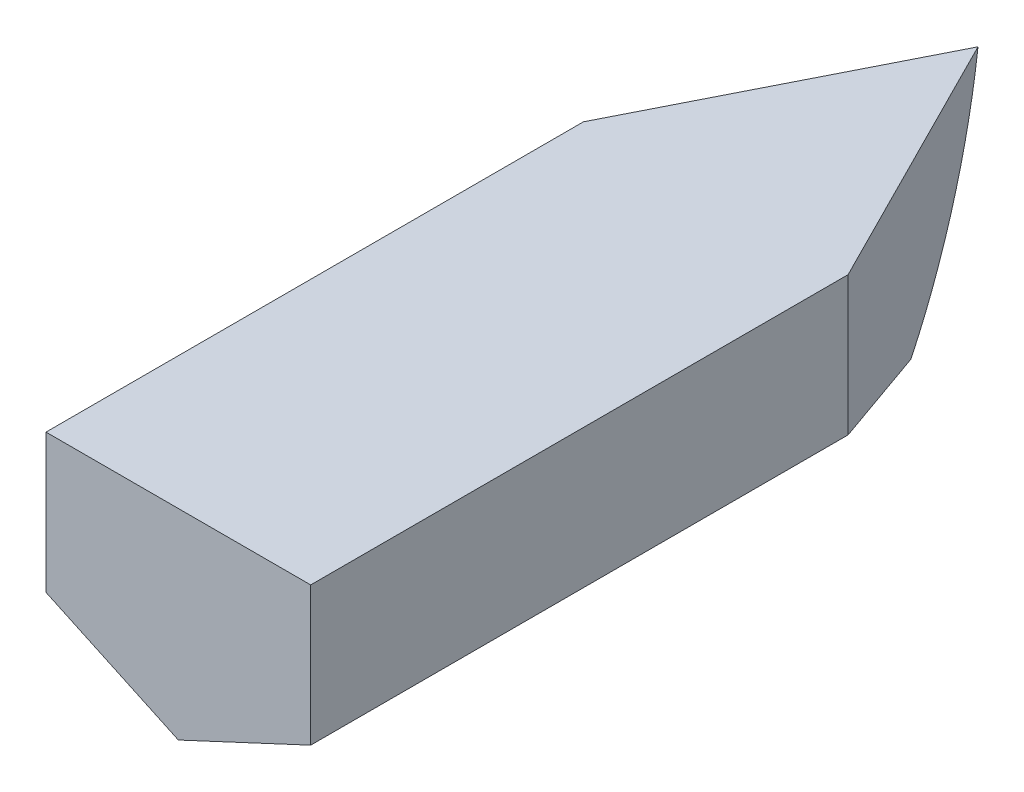
SolidWorks part; units mm, degrees
material "Rubber"
ref_plane "Front Plane" through (0, 0, 0) normal (0, 0, 1) x (1, 0, 0)
ref_plane "Top Plane" through (0, 0, 0) normal (0, 1, 0) x (1, 0, 0)
ref_plane "Right Plane" through (0, 0, 0) normal (1, 0, 0) x (0, 0, -1)
sketch "Cross-Section B Sketch" plane through (0, 0, 0) normal (0, 0, 1) x (1, 0, 0)
  line L5 (-0.0006, -30.4064) -> (37.5282, -12.9064)
  line L6 (37.5282, -12.9064) -> (37.5282, 26.4536)
  line L7 (37.5282, 26.4536) -> (-37.5294, 26.4536)
  line L8 (-37.5294, -12.9064) -> (-37.5294, 26.4536)
  line L9 (-0.0006, -30.4064) -> (-37.5294, -12.9064)
  line L10 (-76.707, -30.4064) -> (84.3947, -30.4064) construction
  dimension "Deadrise Angle" = 25
  dimension "Width" = 75.0576
  dimension "Height" = 56.86
sketch "Fore-Aft" plane through (0, 0, 0) normal (1, 0, 0) x (0, 0, -1)
  line L0 (0, 0) -> (62.0342, 0) construction
  line L1 (76.2, 28.4649) -> (-76.2, 28.4649)
  line L2 (151.4715, 28.4649) -> (76.2, 28.4649)
  line L4 (76.2, -30.4064) -> (-76.2, -30.4064)
  line L6 (-76.2, 28.4649) -> (-76.2, -30.4064)
  line L7 (76.2, -30.4064) -> (76.2, 28.4649)
  point P6 (0, 28.4649)
  point P9 (0, -30.4064)
  dimension "D1" = 152.4
  dimension "D2" = 58.8713
ref_plane "Cross-Section A Plane " through (0, 0, -76.2) normal (0, 0, -1) x (-1, 0, 0)
sketch "Cross-Section A Sketch" plane through (0, 0, -76.2) normal (0, 0, -1) x (-1, 0, 0)
  line L5 (-0.0006, -30.4064) -> (37.5282, -12.9064)
  line L6 (37.5282, -12.9064) -> (37.5282, 26.4536)
  line L7 (37.5282, 26.4536) -> (-37.5294, 26.4536)
  line L8 (-37.5294, -12.9064) -> (-37.5294, 26.4536)
  line L9 (-0.0006, -30.4064) -> (-37.5294, -12.9064)
  line L10 (-76.707, -30.4064) -> (84.3947, -30.4064) construction
  dimension "Deadrise Angle" = 25
  dimension "Width" = 75.0576
  dimension "Height" = 56.86
ref_plane "Cross-Section C Plane" through (0, 0, 76.2) normal (0, 0, -1) x (-1, 0, 0)
sketch "Cross-Section C Sketch" plane through (0, 0, 76.2) normal (0, 0, 1) x (1, 0, 0)
  line L5 (-0.0006, -30.4064) -> (37.5282, -12.9064)
  line L6 (37.5282, -12.9064) -> (37.5282, 26.4536)
  line L7 (37.5282, 26.4536) -> (-37.5294, 26.4536)
  line L8 (-37.5294, -12.9064) -> (-37.5294, 26.4536)
  line L9 (-0.0006, -30.4064) -> (-37.5294, -12.9064)
  line L10 (-76.707, -30.4064) -> (84.3947, -30.4064) construction
  dimension "Deadrise Angle" = 25
  dimension "Width" = 75.0576
  dimension "Height" = 56.86
loft "Fore-Aft Loft" add profiles "Cross-Section C Sketch", "Cross-Section B Sketch", "Cross-Section A Sketch"
sketch "Port-Starboard Profile" plane through (0, 0, 0) normal (1, 0, 0) x (0, 0, -1)
  line L4 (76.2, 26.4536) -> (-76.2, 26.4536) construction
  line L5 (76.2, 26.4536) -> (-76.2, 26.4536) construction
  line L7 (150.5603, 26.4536) -> (150.5603, -30.4064)
  line L8 (76.2, -30.4064) -> (150.5603, -30.4064)
  arc A1 (76.2, -30.4064) -> (150.5603, 26.4536) centre (75.8165, 47.1485) ccw
  dimension "Bow Curve Radius" = 77.5558
  dimension "Bow Length" = 74.3603
sketch "Top Bow Profile" plane through (0, 26.4536, 0) normal (0, 1, 0) x (1, 0, 0)
  line L0 (37.5294, 76.2) -> (0, 150.5603)
  line L1 (0, 76.2) -> (0, 150.5603) construction
  line L3 (-37.5282, 76.2) -> (37.5294, 76.2)
  line L4 (0, 150.5603) -> (-37.5282, 76.2)
extrude "Top Bow Extrusion" add sketch "Top Bow Profile" against normal up to vertex (56.86 mm away) up to point (0, -30.4064, -150.5603)
extrude "Port-Starboard Cut" cut sketch "Port-Starboard Profile" against normal through all both and the other way through all contours A1 L8 L7
sketch "Fore-Aft Bow Construction Sketch" plane through (0, 0, -76.2) normal (0, 0, 1) x (1, 0, 0)
  line L0 (37.5294, -30.4064) -> (37.5294, -12.9064) construction
  line L1 (37.5294, -12.9064) -> (0.0006, -30.4064) construction
  line L2 (0.0006, -30.4064) -> (37.5294, -30.4064) construction
  line L3 (-37.5282, -30.4064) -> (0.0006, -30.4064) construction
  line L4 (0.0006, -30.4064) -> (-37.5282, -12.9064) construction
  line L5 (-37.5282, -12.9064) -> (-37.5282, -30.4064) construction
  line L6 (37.5294, -30.4064) -> (37.5294, -12.9064)
  line L7 (37.5294, -12.9064) -> (0.0006, -30.4064)
  line L8 (0.0006, -30.4064) -> (37.5294, -30.4064)
  line L9 (-37.5282, -30.4064) -> (0.0006, -30.4064)
  line L10 (0.0006, -30.4064) -> (-37.5282, -12.9064)
  line L11 (-37.5282, -12.9064) -> (-37.5282, -30.4064)
extrude "Fore-aft bow wrapup extrustion" cut sketch "Fore-Aft Bow Construction Sketch" against normal up to next contours L7 L8 L6
scale "Scale" scale about centroid uniform scaling yes scale factor 2
shell "Shell2" thickness 2.54
